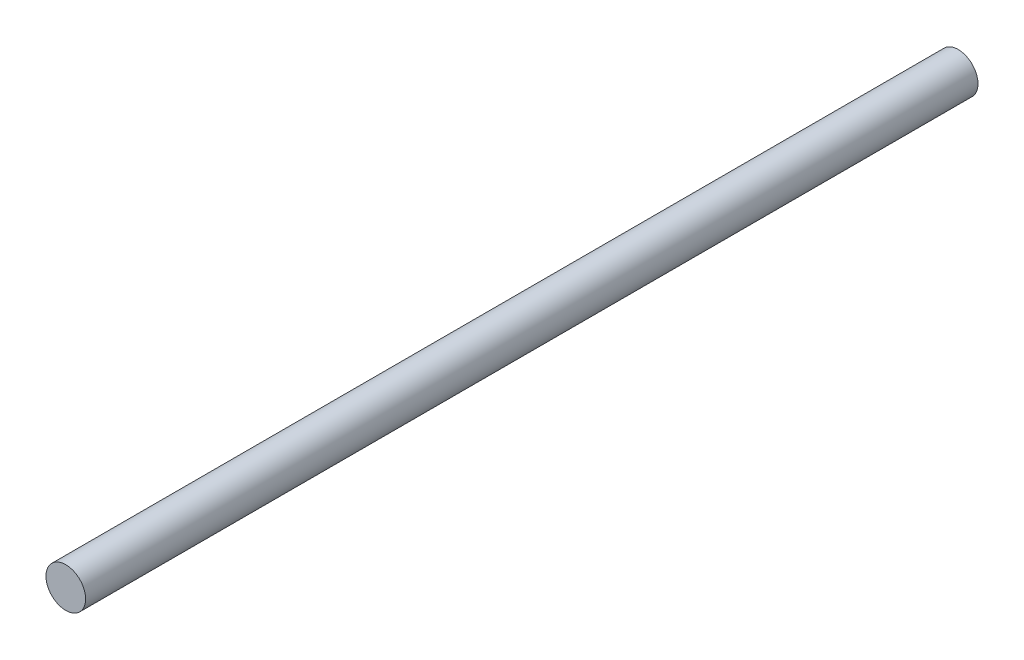
SolidWorks part; units mm, degrees
ref_plane "Alzado" through (0, 0, 0) normal (0, 0, 1) x (1, 0, 0)
ref_plane "Planta" through (0, 0, 0) normal (0, 1, 0) x (1, 0, 0)
ref_plane "Vista lateral" through (0, 0, 0) normal (1, 0, 0) x (0, 0, -1)
sketch "Croquis1" plane through (0, 0, 0) normal (0, 0, 1) x (1, 0, 0)
  circle A0 centre (0, 0) radius 10
  dimension "D1" = 20
extrude "Saliente-Extruir2" add sketch "Croquis1" along normal blind 450
